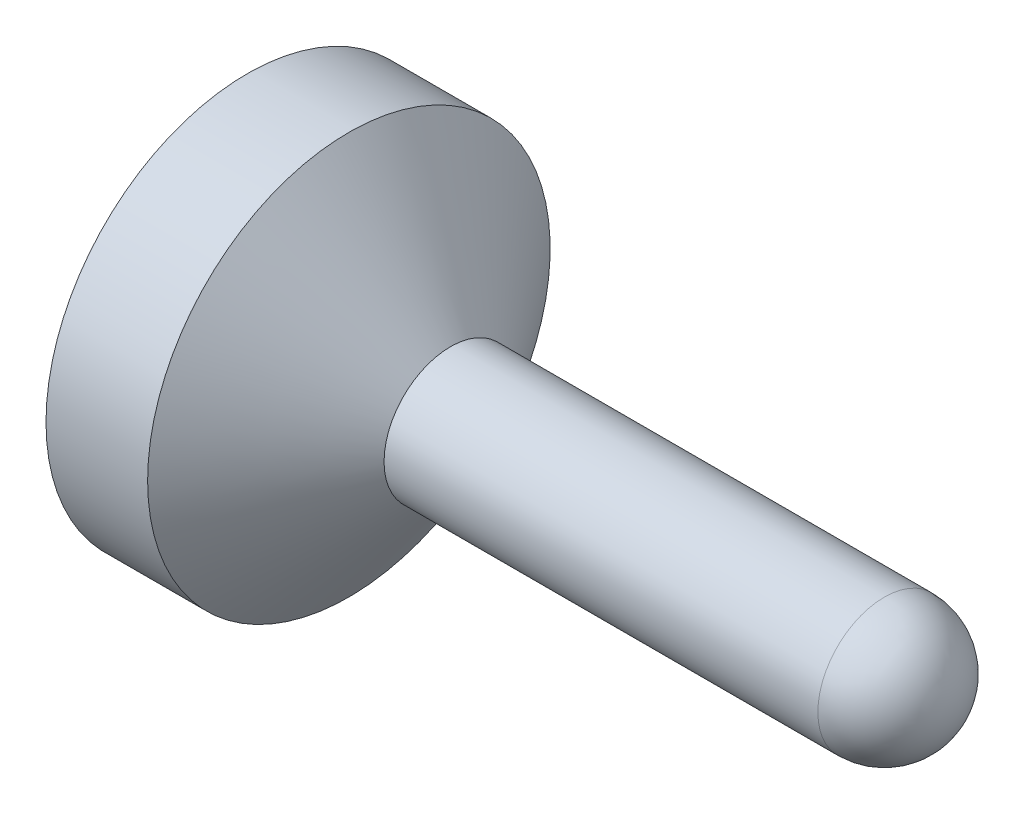
SolidWorks part; units mm, degrees
material "Brass Alloy 385"
ref_plane "Front Plane" through (0, 0, 0) normal (0, 0, 1) x (1, 0, 0)
ref_plane "Top Plane" through (0, 0, 0) normal (0, 1, 0) x (1, 0, 0)
ref_plane "Right Plane" through (0, 0, 0) normal (1, 0, 0) x (0, 0, -1)
sketch "Sketch1" plane through (0, 0, 0) normal (0, 0, 1) x (1, 0, 0)
  line L0 (0, 0) -> (0, 0.6541)
  line L1 (0, 0.6541) -> (0.3302, 0.6541)
  line L2 (0.3302, 0.6541) -> (0.6604, 0.2159)
  line L3 (0.6604, 0.2159) -> (2.0701, 0.2159)
  line L4 (0, 0) -> (2.286, 0)
  line L5 (0, 0) -> (2.286, 0) construction
  arc A0 (2.286, 0) -> (2.0701, 0.2159) centre (2.0701, 0) ccw
revolve "RevolutionAngle1" add sketch "Sketch1" angle 360 about L5
